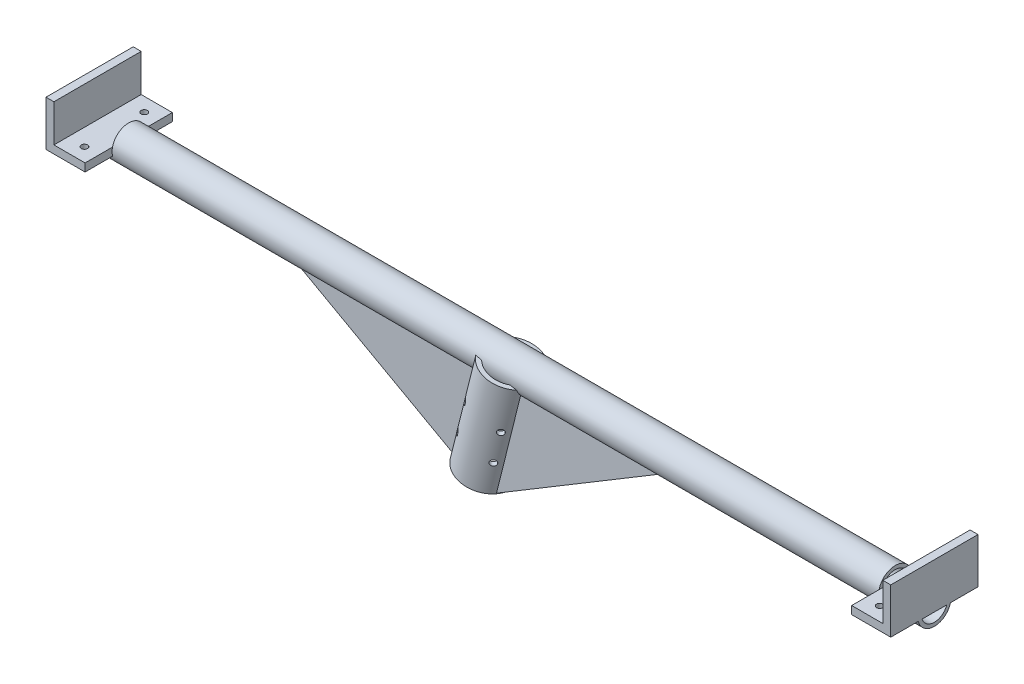
SolidWorks part; units mm, degrees
material "Alloy Steel"
ref_plane "Front" through (0, 0, 0) normal (0, 0, 1) x (1, 0, 0)
ref_plane "Top" through (0, 0, 0) normal (0, 1, 0) x (1, 0, 0)
ref_plane "Right" through (0, 0, 0) normal (1, 0, 0) x (0, 0, -1)
sketch "Sketch1" plane through (0, 0, 0) normal (1, 0, 0) x (0, 0, -1)
  circle A0 centre (0, 0) radius 13.335
  circle A1 centre (0, 0) radius 10.465
  dimension "D1" = 26.67
  dimension "D2" = 2.87
extrude "Boss-Extrude1" add sketch "Sketch1" along normal blind 338.85
sketch "Sketch4" plane through (338.85, 0, 0) normal (1, 0, 0) x (0, 0, -1)
  line L0 (-12.9932, 3) -> (12.9932, 3)
  arc A0 (12.9932, 3) -> (-12.9932, 3) centre (0, 0) ccw
  circle A1 centre (0, 0) radius 13.335 construction
  dimension "D1" = 3
extrude "Cut-Extrude3" cut sketch "Sketch4" against normal blind 25 from offset 6.35 offset against normal yes
sketch "Sketch5" plane through (0, 3, 0) normal (0, 1, 0) x (1, 0, 0)
  line L0 (332.5, -12.9932) -> (332.5, -10.0258) construction
  line L1 (307.5, 35) -> (332.5, 35)
  line L2 (307.5, 35) -> (307.5, -35)
  line L3 (307.5, -35) -> (332.5, -35)
  line L4 (332.5, 35) -> (332.5, -35)
  line L5 (307.5, 35) -> (332.5, -35) construction
  line L6 (307.5, -35) -> (332.5, 35) construction
  line L7 (307.5, -12.9932) -> (307.5, -10.0258) construction
  point P0 (320, 0)
  dimension "D1" = 70
extrude "Boss-Extrude2" add sketch "Sketch5" against normal blind 6.35
sketch "Sketch6" plane through (0, 3, 0) normal (0, 1, 0) x (1, 0, 0)
  line L0 (332.5, 35) -> (332.5, -35)
  line L1 (332.5, 35) -> (338.85, 35)
  line L2 (332.5, -35) -> (338.85, -35)
  line L3 (338.85, 35) -> (338.85, -35)
  line L4 (338.85, -13.335) -> (338.85, 13.335) construction
extrude "Boss-Extrude3" add sketch "Sketch6" against normal blind 6.35 and the other way blind 30
hole_wizard "#8 (0.199) Diameter Hole1" positions "Sketch8" profile "Sketch7" hole size "#8" standard "ANSI Inch"
sketch "Sketch8" plane through (0, -3.35, 0) normal (0, -1, 0) x (-1, 0, 0)
  line L0 (-338.85, 12.9074) -> (-338.85, -12.9074) construction
  line L1 (-307.5, -12.9074) -> (-307.5, -35) construction
  point P0 (-319, 24)
  point P2 (-319, -24)
  point P5 (-338.85, 0)
  dimension "D1" = 48
  dimension "D2" = 24
  dimension "D3" = 11.5
sketch "Sketch7" plane through (319, -3.35, -24) normal (1, 0, 0) x (0, 0, -1)
  line L0 (0, 0) -> (0, 32.41)
  line L1 (0, 32.41) -> (2.5273, 32.41)
  line L2 (2.5273, 32.41) -> (2.5273, 0)
  line L5 (2.5273, 0) -> (0, 0)
  line L10 (0, 32.41) -> (-2.5273, 32.41) construction
  line L11 (0, -6.35) -> (0, 107.95) construction
  dimension "Hole Dia." = 5.0546
  dimension "Hole Depth" = 32.41
  dimension "Drill Angle" = 180
mirror "Mirror1" about plane through (0, 0, 0) normal (1, 0, 0) of "Boss-Extrude1", "Cut-Extrude3", "Boss-Extrude2", "Boss-Extrude3", "#8 (0.199) Diameter Hole1"
sketch "Sketch9" plane through (0, 0, 0) normal (0, 0, 1) x (1, 0, 0)
  line L0 (0, 0) -> (-117.4227, 0) construction
  line L1 (0, 0) -> (8.2085, 32.9226) construction
  dimension "D1" = 76
ref_plane "Plane1" through (0, 0, 0) normal (0.2419, 0.9703, 0) x (0.9703, -0.2419, 0)
ref_plane "Plane2" through (0, -13, 0) normal (0, 1, 0) x (1, 0, 0)
sketch "Sketch10" plane through (0, 0, 0) normal (0.2419, 0.9703, 0) x (0.9703, -0.2419, 0)
  circle A0 centre (0, 0) radius 17.52
  circle A1 centre (0, 0) radius 21.082
  dimension "D1" = 35.04
  dimension "D2" = 42.164
extrude "Boss-Extrude4" add sketch "Sketch10" against normal blind 85
sketch "Sketch13" plane through (-20.5634, -82.4751, 0) normal (-0.2419, -0.9703, 0) x (0.9703, -0.2419, 0)
  line L0 (-14.9072, 14.9072) -> (0, 0) construction
  line L1 (0, 0) -> (14.9072, 14.9072) construction
  line L2 (50, 0) -> (-50, 0) construction
  dimension "D1" = 45
hole_wizard "#8 (0.199) Diameter Hole2" positions "3DSketch4" profile "Sketch12" hole size "#8" standard "ANSI Inch"
sketch3d "3DSketch4"
  line L0 (-35.0278, -78.8688, 14.9072) -> (-20.5634, -82.4751, 0) construction
  line L1 (-20.5634, -82.4751, 0) -> (-6.0989, -86.0815, 14.9072) construction
  point P0 (-28.9797, -54.6114, 14.9072)
  point P10 (-0.0509, -61.8241, 14.9072)
  point P17 (-22.9317, -30.354, 14.9072)
  point P19 (5.9972, -37.5667, 14.9072)
  dimension "D7" = 50
  dimension "D1" = 25
  dimension "D2" = 25
  dimension "D3" = 25
  dimension "D4" = 25
  dimension "D5" = 50
  dimension "D6" = 50
  dimension "D8" = 50
sketch "Sketch12" plane through (-28.9797, -54.6114, 14.9072) normal (0.6286, 0.6286, 0.4579) x (0.3662, -0.7587, 0.5388)
  line L0 (0, 0) -> (0, 50)
  line L1 (0, 50) -> (2.5273, 50)
  line L2 (2.5273, 50) -> (2.5273, 0)
  line L5 (2.5273, 0) -> (0, 0)
  line L10 (0, 50) -> (-2.5273, 50) construction
  line L11 (0, -6.35) -> (0, 107.95) construction
  dimension "Hole Dia." = 5.0546
  dimension "Hole Depth" = 50
  dimension "Drill Angle" = 180
sketch "Sketch17" plane through (0, 0, 0) normal (0, 0, 1) x (1, 0, 0)
  line L0 (119.2042, -13.335) -> (0.6404, -84.5753)
  line L26 (18.4026, -13.335) -> (338.85, -13.335) construction
  line L27 (-0.1076, -87.5753) -> (18.4026, -13.335) construction
  dimension "D1" = 45
  dimension "D2" = 3
rib "Rib3" sketch "Sketch17" sketch "Sketch17" thickness 20 extrusion direction parallel to sketch draft on no parameters "D1"=20
sketch "Sketch18" plane through (0, 0, 0) normal (0, 0, 1) x (1, 0, 0)
  line L0 (-150.5731, -13.335) -> (-40.2934, -74.4641)
  line L1 (-338.85, -13.335) -> (-25.0522, -13.335) construction
  line L28 (-25.0522, -13.335) -> (-41.0191, -77.3749) construction
  dimension "D1" = 75
  dimension "D2" = 3
rib "Rib4" sketch "Sketch18" sketch "Sketch18" thickness 20 extrusion direction parallel to sketch draft on no parameters "D1"=20
sketch "Sketch19" plane through (338.85, 0, 0) normal (1, 0, 0) x (0, 0, -1)
  line L0 (-35, 33) -> (35, 33)
  line L1 (35, 33) -> (35, -3.35) construction
  line L2 (35, 33) -> (35, 63)
  line L3 (35, 63) -> (-35, 63)
  line L4 (-35, 63) -> (-35, 33)
  dimension "D1" = 90
  dimension "D2" = 30
extrude "Boss-Extrude5" [suppressed] add sketch "Sketch19" against normal blind 678
